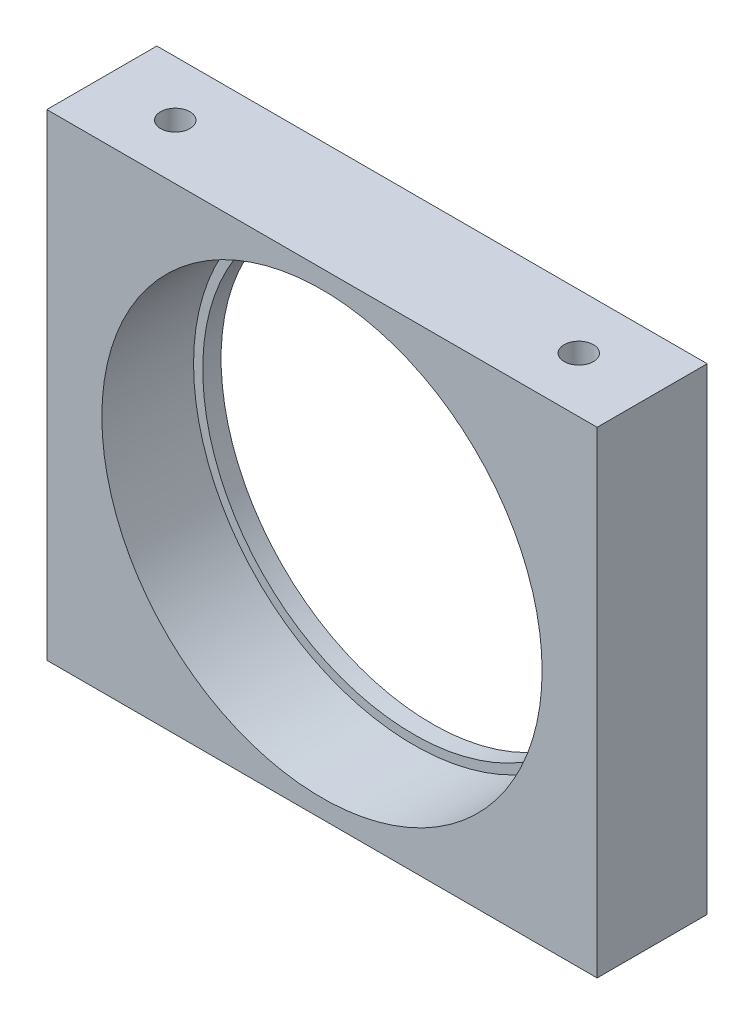
SolidWorks part; units mm, degrees
material "Alliage 1060"
ref_plane "Plan de face" through (0, 0, 0) normal (0, 0, 1) x (1, 0, 0)
ref_plane "Plan de dessus" through (0, 0, 0) normal (0, 1, 0) x (1, 0, 0)
ref_plane "Plan de droite" through (0, 0, 0) normal (1, 0, 0) x (0, 0, -1)
sketch "Esquisse1" plane through (0, 0, 0) normal (0, 0, 1) x (1, 0, 0)
  line L1 (0, 0) -> (30, 0)
  line L2 (0, 0) -> (0, 26)
  line L3 (0, 26) -> (30, 26)
  line L4 (30, 0) -> (30, 26)
  circle A0 centre (15, 13) radius 11.5
  dimension "D3" = 23
  dimension "D1" = 26
  dimension "D2" = 30
  dimension "D4" = 15
  dimension "D5" = 13
extrude "Boss.-Extru.1" add sketch "Esquisse1" along normal blind 6
sketch "Esquisse2" plane through (0, 0, 6) normal (0, 0, 1) x (1, 0, 0)
  line L0 (0, 26) -> (0, 0) construction
  line L1 (30, 26) -> (0, 26) construction
  circle A0 centre (15, 13) radius 12
  dimension "D1" = 24
  dimension "D2" = 15
  dimension "D3" = 13
extrude "Enlèv. mat.-Extru.1" cut sketch "Esquisse2" against normal blind 5
hole_wizard "Trou pour taraudage pour trou taraudé M21" positions "Esquisse3" profile "Esquisse4" hole size "M2" standard "ISO"
sketch "Esquisse3" plane through (0, 26, 0) normal (0, 1, 0) x (1, 0, 0)
  line L0 (0, -6) -> (0, 0) construction
  line L1 (30, -6) -> (30, 0) construction
  line L3 (30, 0) -> (0, 0) construction
  point P0 (4, -3)
  point P2 (26, -3)
  dimension "D1" = 4
  dimension "D2" = 4
  dimension "D3" = 3
  dimension "D4" = 3
sketch "Esquisse4" plane through (4, 26, 3) normal (1, 0, 0) x (0, 0, 1)
  line L0 (0, 0) -> (0, 5.4807)
  line L1 (0, 5.4807) -> (0.8, 5)
  line L2 (0.8, 5) -> (0.8, 0)
  line L5 (0.8, 0) -> (0, 0)
  line L10 (0, 5.4807) -> (-0.8, 5) construction
  line L11 (0, -6.35) -> (0, 107.95) construction
  dimension "Diamètre du perçage" = 1.6
  dimension "Profondeur du perçage" = 5
  dimension "Angle de pointe" = 118
hole_wizard "Trou pour taraudage pour trou taraudé M22" positions "Esquisse5" profile "Esquisse6" hole size "M2" standard "ISO"
sketch "Esquisse5" plane through (0, 0, 0) normal (0, -1, 0) x (-1, 0, 0)
  line L0 (0, 0) -> (-30, 0) construction
  line L1 (0, -6) -> (0, 0) construction
  line L2 (-30, -6) -> (-30, 0) construction
  point P0 (-4, -3)
  point P2 (-26, -3)
  dimension "D1" = 3
  dimension "D3" = 4
  dimension "D4" = 4
sketch "Esquisse6" plane through (4, 0, 3) normal (1, 0, 0) x (0, 0, -1)
  line L0 (0, 0) -> (0, 5.4807)
  line L1 (0, 5.4807) -> (0.8, 5)
  line L2 (0.8, 5) -> (0.8, 0)
  line L5 (0.8, 0) -> (0, 0)
  line L10 (0, 5.4807) -> (-0.8, 5) construction
  line L11 (0, -6.35) -> (0, 107.95) construction
  dimension "Diamètre du perçage" = 1.6
  dimension "Profondeur du perçage" = 5
  dimension "Angle de pointe" = 118
equation "\"D4@Esquisse1\"=\"D2@Esquisse1\"/2"
equation "\"D5@Esquisse1\"=\"D1@Esquisse1\"/2"
equation "\"D2@Esquisse2\"=\"D4@Esquisse1\""
equation "\"D3@Esquisse2\"=\"D5@Esquisse1\""
equation "\"D3@Esquisse3\"=\"D1@Boss.-Extru.1\"/2"
equation "\"D4@Esquisse3\"=\"D1@Boss.-Extru.1\"/2"
equation "\"D1@Esquisse5\"=\"D1@Boss.-Extru.1\"/2"
equation "\"D2@Esquisse5\"=\"D1@Boss.-Extru.1\"/2"
